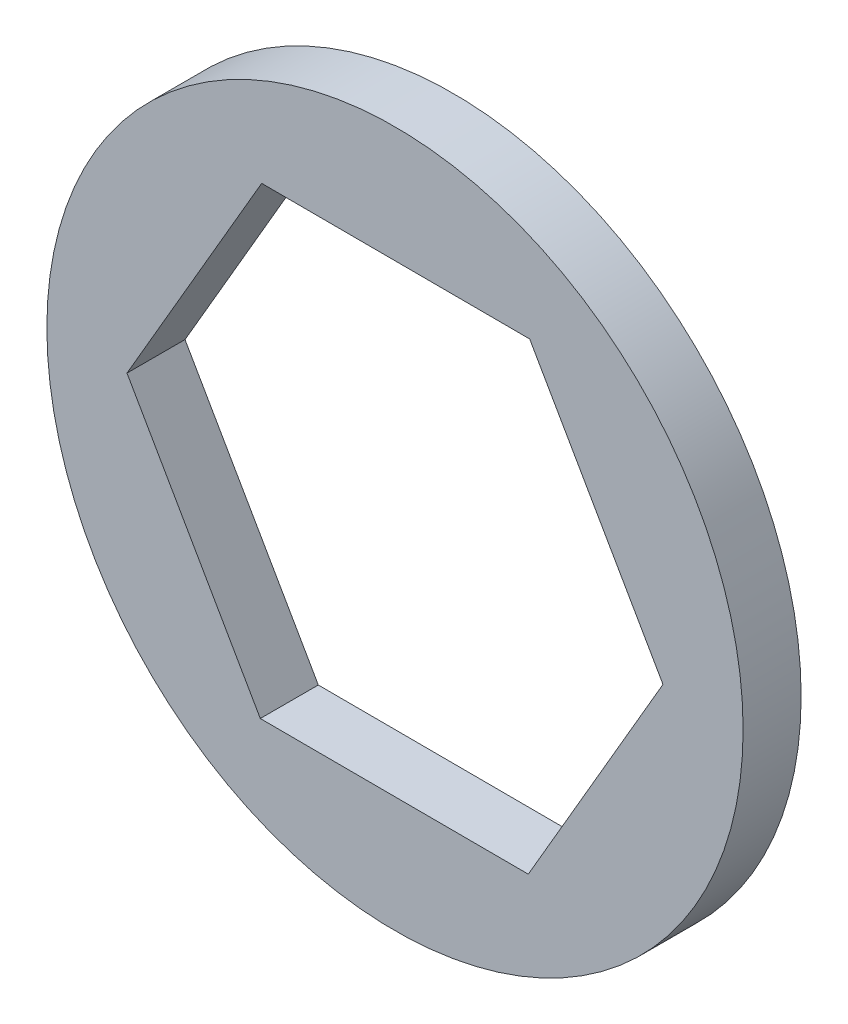
SolidWorks part; units mm, degrees
material "PET"
ref_plane "Front Plane" through (0, 0, 0) normal (0, 0, 1) x (1, 0, 0)
ref_plane "Top Plane" through (0, 0, 0) normal (0, 1, 0) x (1, 0, 0)
ref_plane "Right Plane" through (0, 0, 0) normal (1, 0, 0) x (0, 0, -1)
sketch "Sketch1" plane through (0, 0, 0) normal (0, 0, 1) x (1, 0, 0)
  line L1 (3.647, -6.361) -> (7.3323, -0.0221)
  line L2 (7.3323, -0.0221) -> (3.6853, 6.3389)
  line L3 (3.6853, 6.3389) -> (-3.647, 6.361)
  line L4 (-3.647, 6.361) -> (-7.3323, 0.0221)
  line L5 (-7.3323, 0.0221) -> (-3.6853, -6.3389)
  line L6 (-3.6853, -6.3389) -> (3.647, -6.361)
  circle A0 centre (0, 0) radius 9.525
  circle A1 centre (0, 0) radius 6.35 construction
  dimension "D1" = 19.05
  dimension "D2" = 12.7
extrude "Boss-Extrude1" add sketch "Sketch1" along normal blind 1.5875
